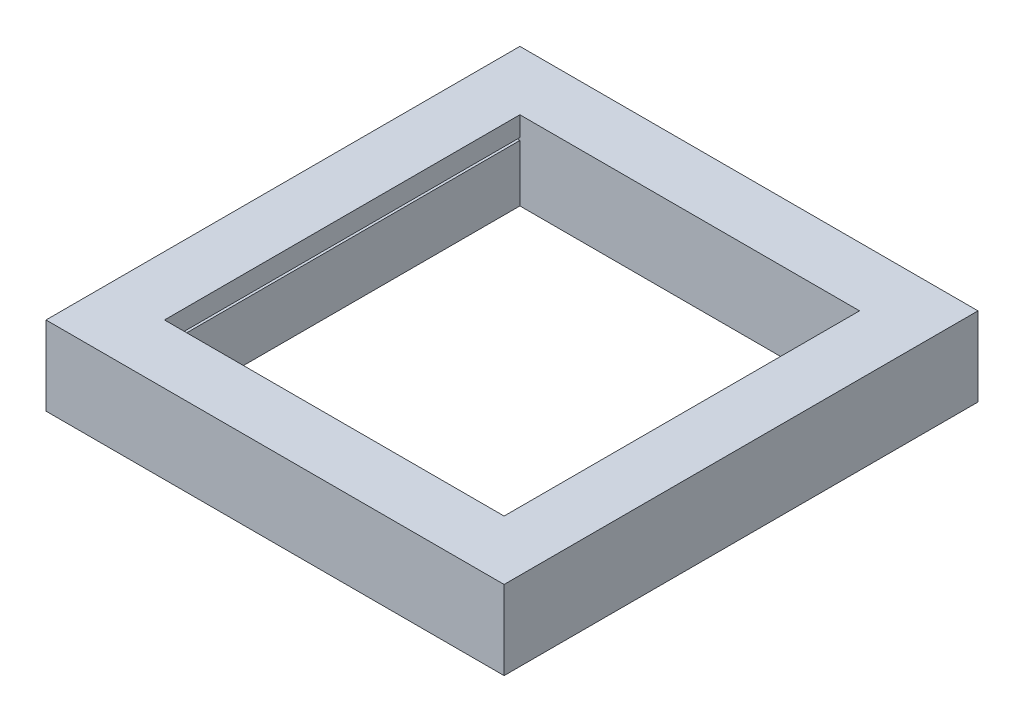
SolidWorks part; units mm, degrees
ref_plane "Front Plane" through (0, 0, 0) normal (0, 0, 1) x (1, 0, 0)
ref_plane "Top Plane" through (0, 0, 0) normal (0, 1, 0) x (1, 0, 0)
ref_plane "Right Plane" through (0, 0, 0) normal (1, 0, 0) x (0, 0, -1)
sketch "Sketch1" plane through (0, 0, 0) normal (0, 1, 0) x (1, 0, 0)
  line L1 (-114.3, -114.3) -> (114.3, -114.3)
  line L2 (-114.3, -114.3) -> (-114.3, 114.3)
  line L3 (-114.3, 114.3) -> (114.3, 114.3)
  line L4 (114.3, -114.3) -> (114.3, 114.3)
  line L5 (-114.3, -114.3) -> (114.3, 114.3) construction
  line L6 (-114.3, 114.3) -> (114.3, -114.3) construction
  line L7 (-147.32, 152.4) -> (-109.22, 152.4)
  line L8 (-147.32, 152.4) -> (-147.32, -152.4)
  line L9 (-147.32, -152.4) -> (-109.22, -152.4)
  line L10 (-109.22, 152.4) -> (-109.22, -152.4)
  line L11 (109.22, 152.4) -> (147.32, 152.4)
  line L12 (109.22, 152.4) -> (109.22, -152.4)
  line L13 (109.22, -152.4) -> (147.32, -152.4)
  line L14 (147.32, 152.4) -> (147.32, -152.4)
  line L15 (-109.22, -152.4) -> (109.22, -152.4)
  line L16 (-109.22, -152.4) -> (-109.22, -114.3)
  line L17 (-109.22, -114.3) -> (109.22, -114.3)
  line L18 (109.22, -152.4) -> (109.22, -114.3)
  line L19 (-109.22, 152.4) -> (109.22, 152.4)
  line L20 (-109.22, 152.4) -> (-109.22, 114.3)
  line L21 (-109.22, 114.3) -> (109.22, 114.3)
  line L22 (109.22, 152.4) -> (109.22, 114.3)
  point P0 (0, 0)
  dimension "D1" = 228.6
  dimension "D2" = 5.08
  dimension "D3" = 5.08
  dimension "D4" = 38.1
  dimension "D5" = 38.1
  dimension "D6" = 38.1
sketch "Sketch2" plane through (0, 0, 0) normal (0, 1, 0) x (1, 0, 0)
  line L1 (-147.32, 152.4) -> (-109.22, 152.4)
  line L2 (-147.32, 152.4) -> (-147.32, -152.4)
  line L3 (-147.32, -152.4) -> (-109.22, -152.4)
  line L4 (-109.22, 152.4) -> (-109.22, -152.4)
  line L5 (109.22, -152.4) -> (147.32, -152.4)
  line L6 (109.22, -152.4) -> (109.22, 152.4)
  line L7 (109.22, 152.4) -> (147.32, 152.4)
  line L8 (147.32, -152.4) -> (147.32, 152.4)
  line L9 (-109.22, 152.4) -> (109.22, 152.4)
  line L11 (-109.22, 114.3) -> (109.22, 114.3)
  line L13 (-109.22, -152.4) -> (109.22, -152.4)
  line L15 (-109.22, -114.3) -> (109.22, -114.3)
extrude "Boss-Extrude1" add sketch "Sketch2" along normal blind 50.8 contours L4 L1 L2 L3 | L5 L8 L7 L6 | L15 L4 L13 L6 | L4 L11 L6 L9
sketch "Sketch4" plane through (-109.22, 0, 0) normal (1, 0, 0) x (0, 0, -1)
  line L1 (-114.3, 38.1) -> (114.3, 38.1)
  line L2 (-114.3, 38.1) -> (-114.3, 36.4998)
  line L3 (-114.3, 36.4998) -> (114.3, 36.4998)
  line L4 (114.3, 38.1) -> (114.3, 36.4998)
  line L5 (114.3, 50.8) -> (114.3, 0) construction
  line L6 (114.3, 50.8) -> (-114.3, 50.8) construction
  dimension "D1" = 1.6002
  dimension "D2" = 12.7
extrude "Cut-Extrude1" cut sketch "Sketch4" against normal blind 5.08
sketch "Sketch6" plane through (0, 0, 0) normal (0, 1, 0) x (1, 0, 0)
  line L0 (0, 182.8085) -> (0, -202.067) construction
mirror "Mirror1" about plane through (0, 0, 0) normal (1, 0, 0) of "Cut-Extrude1"
